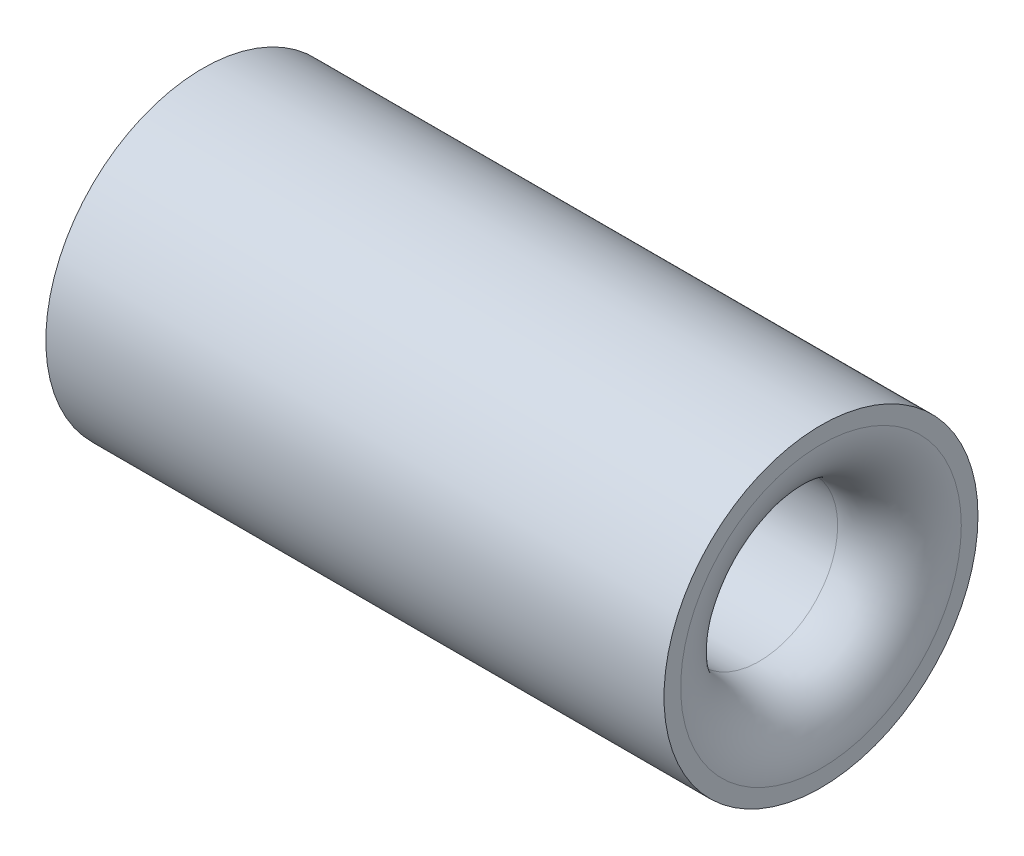
SolidWorks part; units mm, degrees
material "6061 Alloy"
ref_plane "Front Plane" through (0, 0, 0) normal (0, 0, 1) x (1, 0, 0)
ref_plane "Top Plane" through (0, 0, 0) normal (0, 1, 0) x (1, 0, 0)
ref_plane "Right Plane" through (0, 0, 0) normal (1, 0, 0) x (0, 0, -1)
sketch "Sketch1" plane through (0, 0, 0) normal (1, 0, 0) x (0, 0, -1)
  circle A0 centre (0, 0) radius 12.7
  dimension "D1" = 25.4
extrude "Boss-Extrude1" add sketch "Sketch1" along normal blind 50
sketch "Sketch2" plane through (50, 0, 0) normal (1, 0, 0) x (0, 0, -1)
  circle A0 centre (0, 0) radius 6.35
extrude "Cut-Extrude1" cut sketch "Sketch2" against normal through all
fillet "Fillet1" radius 5 1 edges at (50, 0, -6.35)
